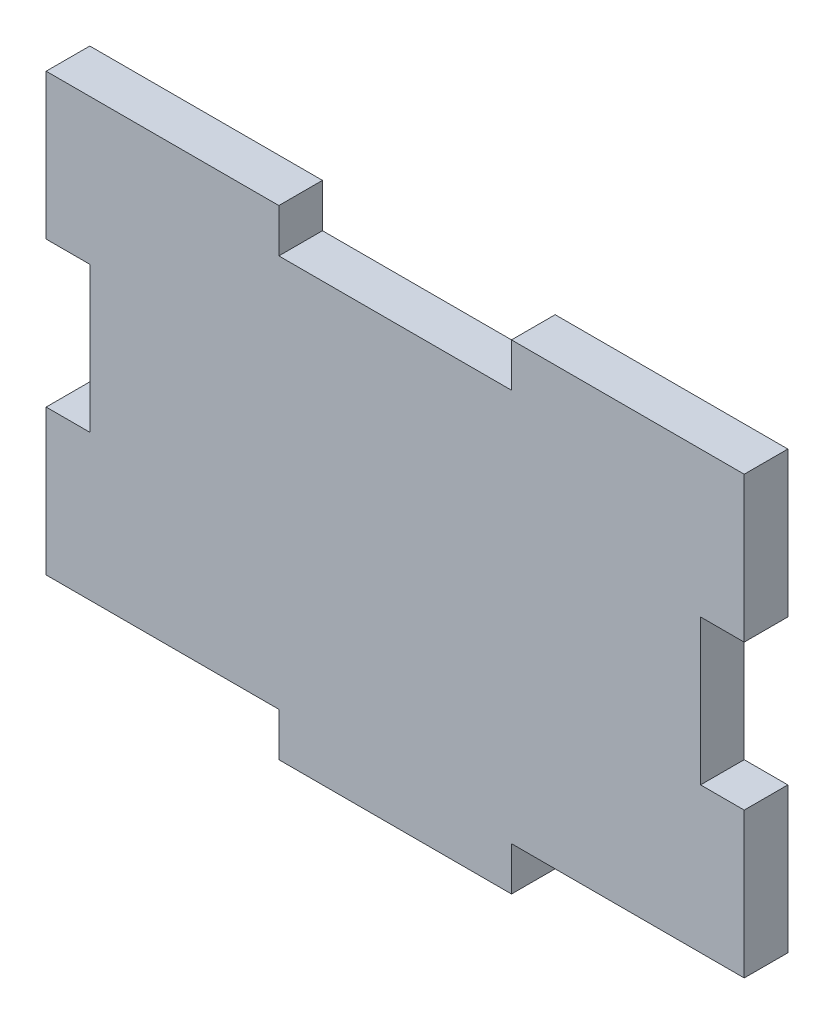
SolidWorks part; units mm, degrees
ref_plane "Alzado" through (0, 0, 0) normal (0, 0, 1) x (1, 0, 0)
ref_plane "Planta" through (0, 0, 0) normal (0, 1, 0) x (1, 0, 0)
ref_plane "Vista lateral" through (0, 0, 0) normal (1, 0, 0) x (0, 0, -1)
sketch "Croquis1" plane through (0, 0, 0) normal (0, 0, 1) x (1, 0, 0)
  line L0 (40, 55) -> (40, 48.9607) construction
  line L1 (0, 0) -> (80, 0)
  line L2 (0, 0) -> (0, 55)
  line L3 (0, 55) -> (80, 55)
  line L4 (80, 0) -> (80, 55)
  line L5 (0, 55) -> (5, 55)
  line L6 (0, 55) -> (0, 0)
  line L7 (0, 0) -> (5, 0)
  line L8 (5, 55) -> (5, 0)
  line L9 (0, 0) -> (80, 0)
  line L10 (0, 0) -> (0, 5)
  line L11 (0, 5) -> (80, 5)
  line L12 (80, 0) -> (80, 5)
  line L13 (26.6667, 5) -> (26.6667, 0)
  line L14 (53.3333, 5) -> (53.3333, 0)
  line L15 (0, 38.3333) -> (5, 38.3333)
  line L16 (0, 21.6667) -> (5, 21.6667)
  line L17 (75, 55) -> (75, 0)
  line L18 (80, 21.6667) -> (75, 21.6667)
  line L19 (80, 38.3333) -> (75, 38.3333)
  point P19 (53.3333, 2.5)
  dimension "D1" = 80
  dimension "D2" = 55
  dimension "D3" = 5
  dimension "D4" = 5
  dimension "D5" = 16.6667
  dimension "D6" = 16.6667
  dimension "D7" = 26.6667
  dimension "D8" = 26.6667
extrude "Saliente-Extruir1" add sketch "Croquis1" along normal blind 5
sketch "Croquis2" plane through (0, 0, 5) normal (0, 0, 1) x (1, 0, 0)
  line L0 (0, 55) -> (80, 55) construction
  line L1 (53.3333, 55) -> (26.6667, 55)
  line L2 (53.3333, 55) -> (53.3333, 50)
  line L3 (53.3333, 50) -> (26.6667, 50)
  line L4 (26.6667, 55) -> (26.6667, 50)
  line L6 (0, 38.3333) -> (0, 55) construction
  line L7 (80, 38.3333) -> (80, 55) construction
  dimension "D1" = 5
  dimension "D2" = 26.6667
  dimension "D3" = 26.6667
extrude "Cortar-Extruir1" cut sketch "Croquis2" against normal blind 10
